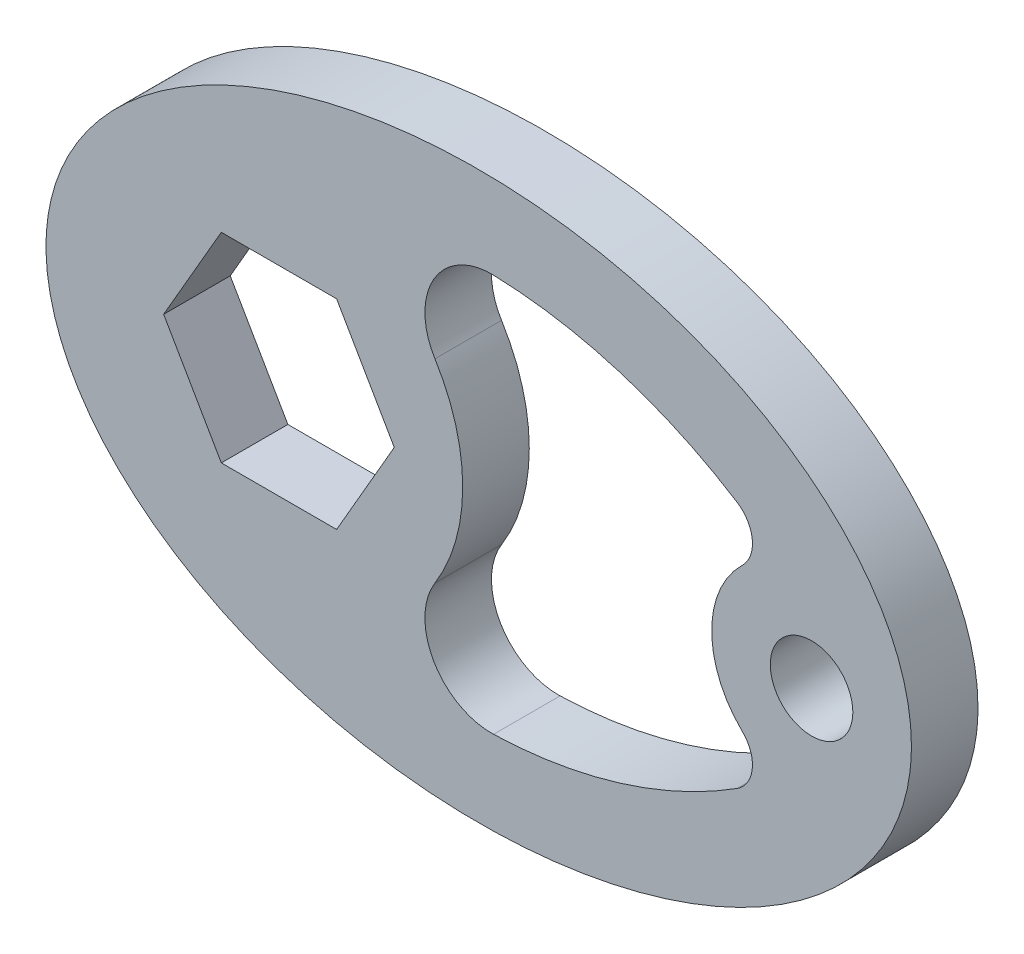
SolidWorks part; units mm, degrees
ref_plane "Front Plane" through (0, 0, 0) normal (0, 0, 1) x (1, 0, 0)
ref_plane "Top Plane" through (0, 0, 0) normal (0, 1, 0) x (1, 0, 0)
ref_plane "Right Plane" through (0, 0, 0) normal (1, 0, 0) x (0, 0, -1)
sketch "Sketch1" plane through (0, 0, 0) normal (0, 0, 1) x (1, 0, 0)
  line L0 (-16.103, 0) -> (-27.1015, 19.05)
  line L1 (-27.1015, 19.05) -> (-49.0985, 19.05)
  line L2 (-49.0985, 19.05) -> (-60.097, 0)
  line L3 (-60.097, 0) -> (-49.0985, -19.05)
  line L4 (-49.0985, -19.05) -> (-27.1015, -19.05)
  line L5 (-27.1015, -19.05) -> (-16.103, 0)
  circle A0 centre (63.5, 0) radius 7.874
  arc A1 (50.2822, 13.7183) -> (50.2822, -13.7183) centre (63.5, 0) ccw
  arc A2 (-8.3425, -18.5239) -> (-8.3425, 18.5239) centre (-38.1, 0) ccw
  arc A4 (49.2795, 23.6521) -> (2.8301, 37.9294) centre (0, -53.975) ccw
  circle A5 centre (-38.1, 0) radius 21.997 construction
  arc A6 (-8.3425, 18.5239) -> (2.8301, 37.9294) centre (2.4392, 25.2355) cw
  arc A7 (50.2822, 13.7183) -> (49.2795, 23.6521) centre (45.8763, 18.2911) ccw
  arc A8 (49.2795, -23.6521) -> (2.8301, -37.9294) centre (0, 53.975) cw
  arc A9 (50.2822, -13.7183) -> (49.2795, -23.6521) centre (45.8763, -18.2911) cw
  arc A10 (-8.3425, -18.5239) -> (2.8301, -37.9294) centre (2.4392, -25.2355) ccw
  ellipse E0 centre (0, 0) end of major axis (82.55, 0) minor radius 53.975
  dimension "D3" = 19.05
  dimension "D4" = 15.748
  dimension "D5" = 6.35
  dimension "D7" = 35.052
  dimension "D8" = 12.7
  dimension "D9" = 6.35
  dimension "D11" = 12.7
  dimension "D12" = 91.948
  dimension "D13" = 19.05
  dimension "D14" = 91.948
  dimension "D1" = 165.1
  dimension "D2" = 107.95
  dimension "D6" = 38.1
  dimension "D10" = 38.1
extrude "Boss-Extrude1" add sketch "Sketch1" along normal blind 12.7
